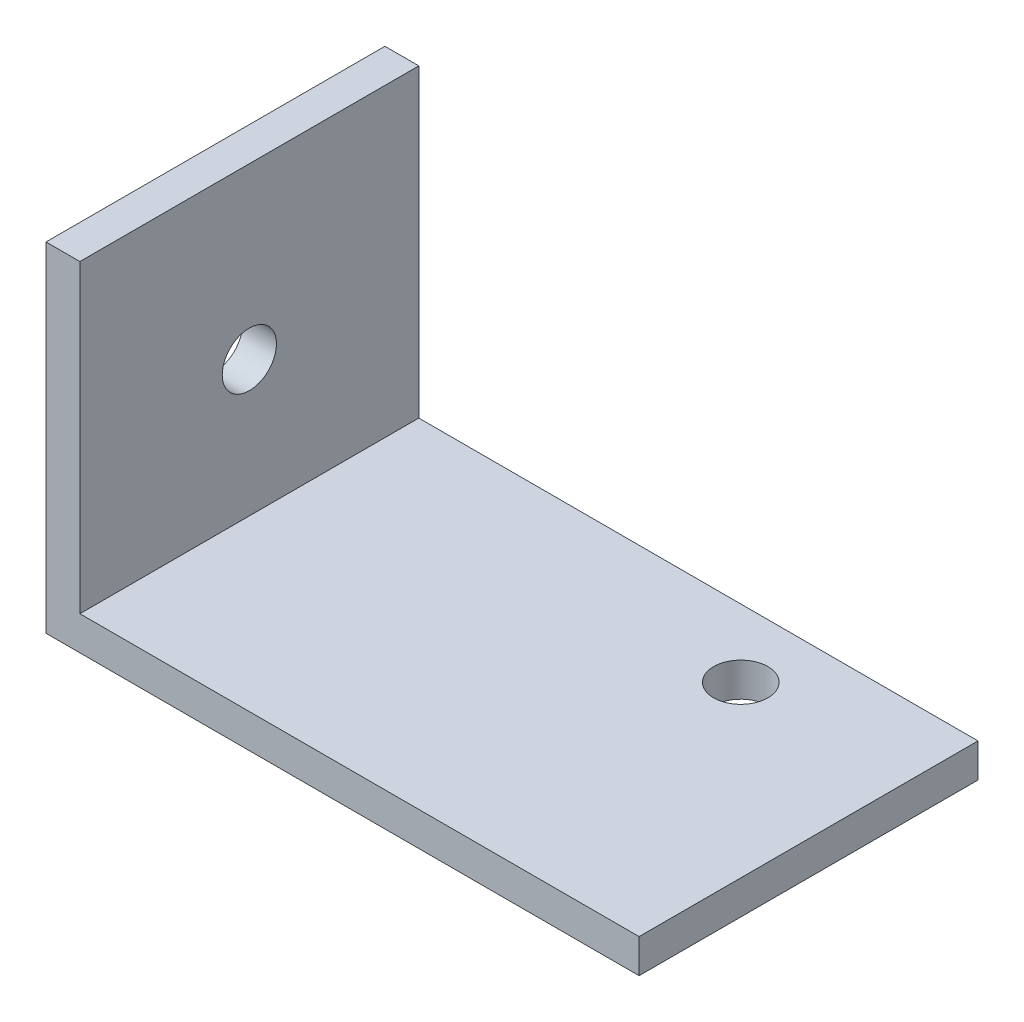
SolidWorks part; units mm, degrees
material "1060 Сплав"
ref_plane "Спереди" through (0, 0, 0) normal (0, 0, 1) x (1, 0, 0)
ref_plane "Сверху" through (0, 0, 0) normal (0, 1, 0) x (1, 0, 0)
ref_plane "Справа" through (0, 0, 0) normal (1, 0, 0) x (0, 0, -1)
sketch "Эскиз1" plane through (0, 0, 0) normal (0, 0, 1) x (1, 0, 0)
  line L0 (0, 0) -> (35, 0)
  line L1 (35, 0) -> (35, 2)
  line L2 (35, 2) -> (2, 2)
  line L3 (2, 2) -> (2, 20)
  line L4 (2, 20) -> (0, 20)
  line L5 (0, 20) -> (0, 0)
  dimension "D1" = 35
  dimension "D2" = 2
  dimension "D3" = 20
extrude "Бобышка-Вытянуть1" add sketch "Эскиз1" along normal blind 20
sketch "Эскиз2" plane through (0, 0, 0) normal (0, -1, 0) x (1, 0, 0)
  arc A0 (26.6, 4) -> (23.4, 4) centre (25, 4) ccw construction
  arc A1 (26.6, 4) -> (23.4, 4) centre (25, 4) ccw construction
  circle A2 centre (25, 4) radius 1.6
extrude "Вырез-Вытянуть1" cut sketch "Эскиз2" against normal through all
sketch "Эскиз3" plane through (0, 0, 0) normal (-1, 0, 0) x (0, 0, 1)
  line L0 (10, 20) -> (10, 0) construction
  line L1 (20, 20) -> (0, 20) construction
  line L2 (20, 0) -> (0, 0) construction
  line L3 (0, 10) -> (20, 10) construction
  line L4 (0, 20) -> (0, 0) construction
  line L5 (20, 20) -> (20, 0) construction
  circle A0 centre (10, 10) radius 1.6
  dimension "D1" = 3.2
extrude "Вырез-Вытянуть2" cut sketch "Эскиз3" against normal through all
